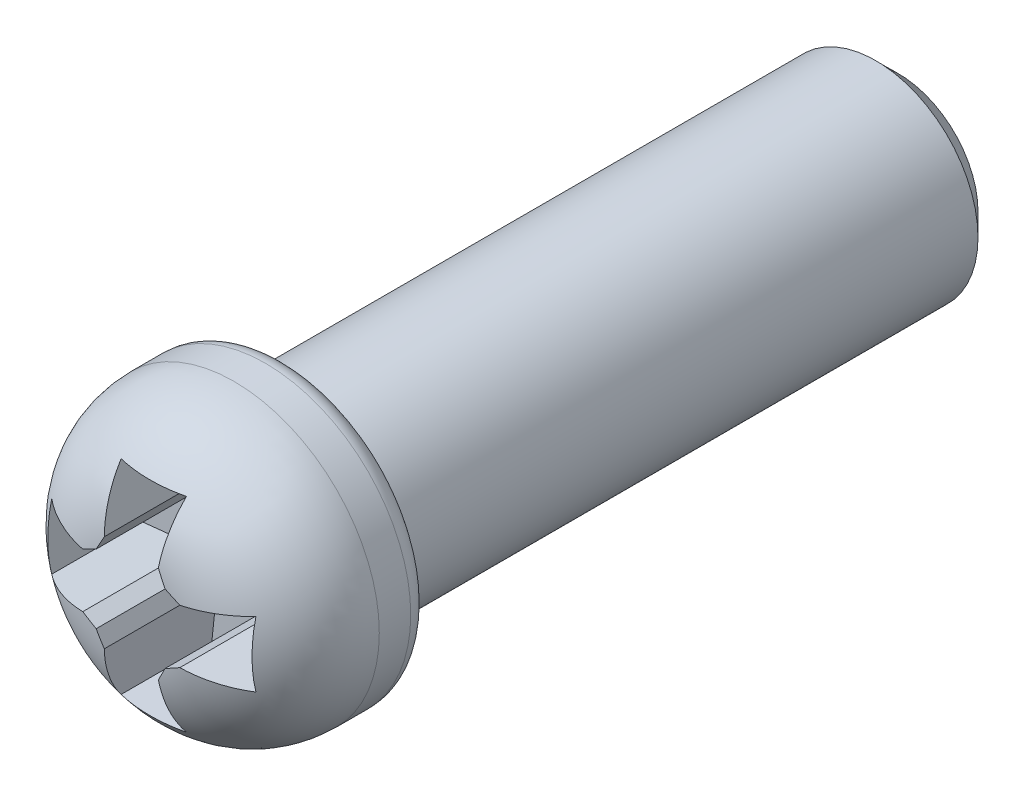
SolidWorks part; units mm, degrees
ref_plane "Front Plane" through (0, 0, 0) normal (0, 0, 1) x (1, 0, 0)
ref_plane "Top Plane" through (0, 0, 0) normal (0, 1, 0) x (1, 0, 0)
ref_plane "Right Plane" through (0, 0, 0) normal (1, 0, 0) x (0, 0, -1)
ref_plane "Plane1" through (0, 0, 0) normal (1, 0, 0) x (0, 0, -1)
sketch "Sketch1" plane through (0, 0, 0) normal (1, 0, 0) x (0, 0, -1)
  line L0 (-1.905, 0) -> (-1.905, 0.508)
  line L1 (-0.635, 1.778) -> (-0.25, 1.778)
  line L2 (0, 1.528) -> (0, 1.25)
  line L3 (0, 1.25) -> (7.224, 1.25)
  line L4 (7.224, 1.25) -> (7.5, 0.974)
  line L5 (7.5, 0.974) -> (7.5, 0)
  line L6 (7.5, 0) -> (-1.905, 0)
  line L7 (7.5, 0) -> (-1.905, 0) construction
  arc A0 (-1.905, 0.508) -> (-0.635, 1.778) centre (-0.635, 0.508) cw
  arc A1 (-0.25, 1.778) -> (0, 1.528) centre (-0.25, 1.528) cw
revolve "Revolve1" add sketch "Sketch1" angle 360 about L7
cosmetic thread "Cosmetic Thread1" parameters "D1"=7.5, "D2"=1.948
ref_plane "Plane2" through (0, 0, 0.508) normal (0, 0, 1) x (1, 0, 0)
sketch "Sketch2" plane through (0, 0, 0.508) normal (0, 0, 1) x (1, 0, 0)
  line L0 (-1.25, 0.4) -> (-1.25, -0.4)
  line L1 (-1.25, -0.4) -> (-0.5941, -0.3311)
  line L2 (-0.5941, -0.3311) -> (-0.422, -0.422)
  line L3 (-0.422, -0.422) -> (-0.3311, -0.5941)
  line L4 (-0.3311, -0.5941) -> (-0.4, -1.25)
  line L5 (-0.4, -1.25) -> (0.4, -1.25)
  line L6 (0.4, -1.25) -> (0.3311, -0.5941)
  line L7 (0.3311, -0.5941) -> (0.422, -0.422)
  line L8 (0.422, -0.422) -> (0.5941, -0.3311)
  line L9 (0.5941, -0.3311) -> (1.25, -0.4)
  line L10 (1.25, -0.4) -> (1.25, 0.4)
  line L11 (1.25, 0.4) -> (0.5941, 0.3311)
  line L12 (0.5941, 0.3311) -> (0.422, 0.422)
  line L13 (0.422, 0.422) -> (0.3311, 0.5941)
  line L14 (0.3311, 0.5941) -> (0.4, 1.25)
  line L15 (0.4, 1.25) -> (-0.4, 1.25)
  line L16 (-0.4, 1.25) -> (-0.3311, 0.5941)
  line L17 (-0.3311, 0.5941) -> (-0.422, 0.422)
  line L18 (-0.422, 0.422) -> (-0.5941, 0.3311)
  line L19 (-0.5941, 0.3311) -> (-1.25, 0.4)
extrude "Cut-Extrude1" cut sketch "Sketch2" along normal blind 1.524
